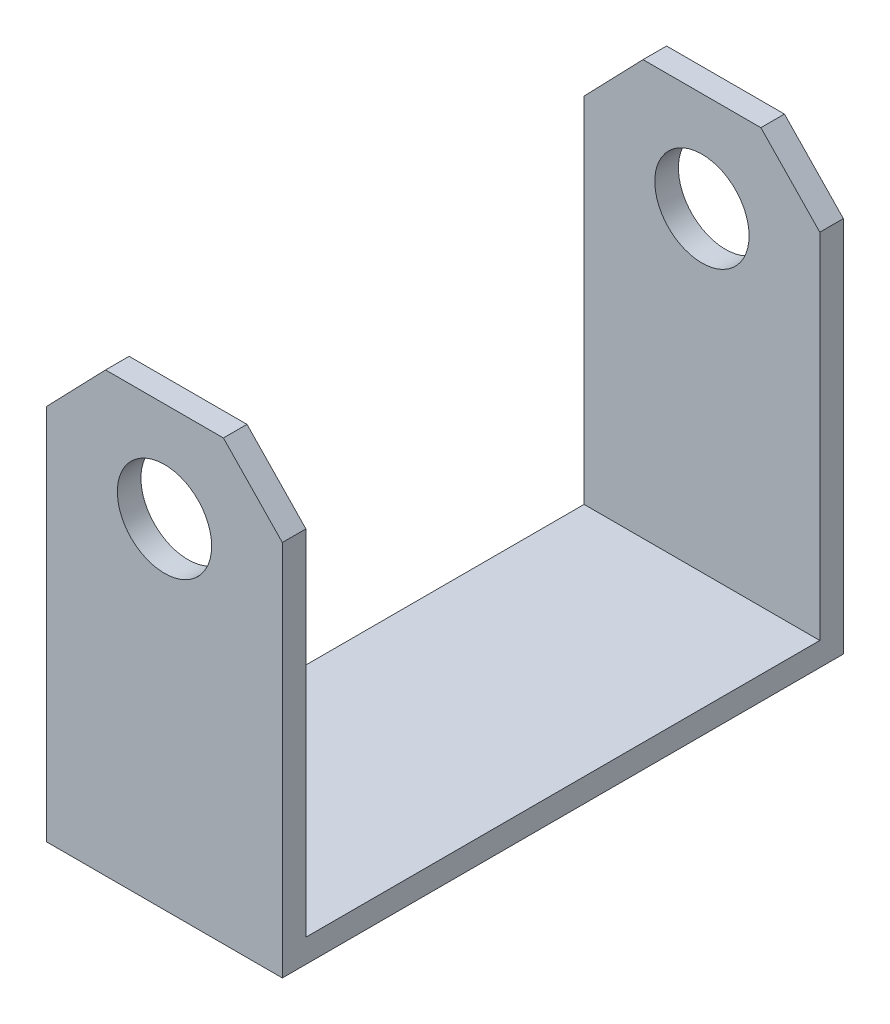
SolidWorks part; units mm, degrees
ref_plane "Front Plane" through (0, 0, 0) normal (0, 0, 1) x (1, 0, 0)
ref_plane "Top Plane" through (0, 0, 0) normal (0, 1, 0) x (1, 0, 0)
ref_plane "Right Plane" through (0, 0, 0) normal (1, 0, 0) x (0, 0, -1)
sketch "Sketch4" plane through (0, 0, 0) normal (0, 0, 1) x (1, 0, 0)
  line L0 (0, 0) -> (12.7, 0)
  line L1 (55, 0) -> (-55, 0) construction
  line L2 (12.7, 0) -> (12.7, 20.32)
  line L3 (12.7, 20.32) -> (9.525, 23.6098)
  line L4 (9.525, 23.6098) -> (3.175, 23.6098)
  line L5 (3.175, 23.6098) -> (0, 20.32)
  line L6 (0, -55) -> (0, 55) construction
  line L7 (0, 20.32) -> (0, 0)
  line L8 (6.35, 0) -> (6.35, 23.6098) construction
  line L9 (0, 20.32) -> (12.7, 20.32) construction
  circle A0 centre (6.35, 18.2461) radius 2.54
  dimension "D2" = 5.08
  dimension "D1" = 4.572
  dimension "D3" = 20.32
  dimension "D4" = 12.7
extrude "Boss-Extrude1" add sketch "Sketch4" along normal blind 1.27
sketch "Sketch5" plane through (0, 0, 1.27) normal (0, 0, 1) x (1, 0, 0)
  line L0 (12.7, 0) -> (12.7, 20.32) construction
  line L1 (0, 0) -> (12.7, 0)
  line L2 (0, 0) -> (0, 1.27)
  line L3 (0, 1.27) -> (12.7, 1.27)
  line L4 (12.7, 0) -> (12.7, 1.27)
  dimension "D1" = 1.27
extrude "Boss-Extrude2" add sketch "Sketch5" along normal blind 28.956
ref_plane "Mirror Plane" through (0, 0, 15.113) normal (0, 0, 1) x (1, 0, 0)
mirror "Mirror1" about plane through (0, 0, 15.113) normal (0, 0, 1) of "Boss-Extrude1"
